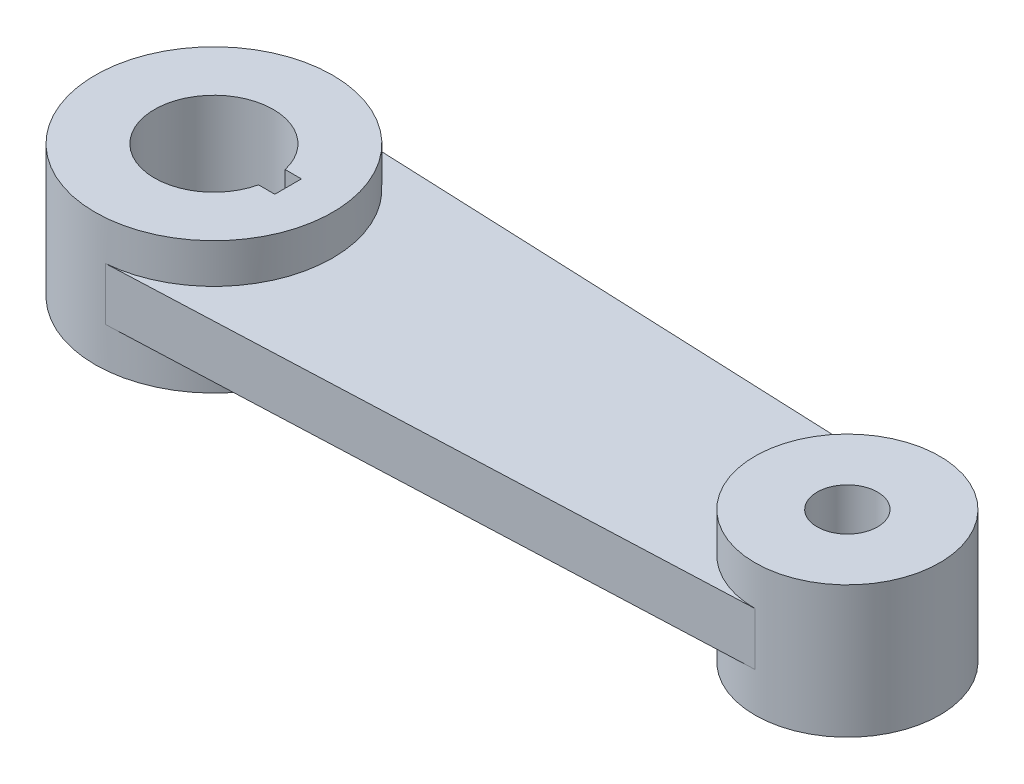
SolidWorks part; units mm, degrees
ref_plane "Front Plane" through (0, 0, 0) normal (0, 0, 1) x (1, 0, 0)
ref_plane "Top Plane" through (0, 0, 0) normal (0, 1, 0) x (1, 0, 0)
ref_plane "Right Plane" through (0, 0, 0) normal (1, 0, 0) x (0, 0, -1)
sketch "Sketch1" plane through (0, 0, 0) normal (0, 1, 0) x (1, 0, 0)
  line L1 (-150, 56.25) -> (150, 43.75)
  line L2 (-114.864, 6.3) -> (-114.864, -6.3)
  line L3 (-122.564, 6.3) -> (-114.864, 6.3)
  line L4 (-114.864, -6.3) -> (-122.564, -6.3)
  line L5 (150, -43.75) -> (-150, -56.25)
  arc A0 (-145.3206, 56.055) -> (-145.3206, -56.055) centre (-150, 0) ccw
  arc A1 (-122.564, 6.3) -> (-122.564, -6.3) centre (-150, 0) ccw
  circle A2 centre (150, 0) radius 21.9
  arc A3 (150, -43.75) -> (150, 43.75) centre (150, 0) ccw
  point P4 (0, 0)
  dimension "D1" = 112.5
  dimension "D2" = 56.3
  dimension "D6" = 43.8
  dimension "D7" = 87.5
  dimension "D4" = 7.7
  dimension "D5" = 12.6
extrude "Boss-Extrude3" add sketch "Sketch1" along normal mid plane 25 contours L5 A3 L1 A0 A1 L3 L2 L4 A2
sketch "Sketch2" plane through (0, 12.5, 0) normal (0, 1, 0) x (1, 0, 0)
  circle A0 centre (150, 0) radius 43.75
  circle A1 centre (-150, 0) radius 56.25
  dimension "D1" = 87.5
  dimension "D2" = 112.5
extrude "Boss-Extrude4" add sketch "Sketch2" along normal blind 18.75 and the other way blind 43.75
sketch "Sketch3" plane through (0, 31.25, 0) normal (0, 1, 0) x (1, 0, 0)
  line L0 (-114.864, -6.3) -> (-114.864, 6.3)
  line L1 (-122.564, -6.3) -> (-114.864, -6.3)
  line L2 (-122.564, 6.3) -> (-114.864, 6.3)
  circle A0 centre (150, 0) radius 14.301
  arc A1 (-122.564, 6.3) -> (-122.564, -6.3) centre (-150, 0) ccw
  dimension "D1" = 28.602
  dimension "D2" = 56.3
  dimension "D3" = 12.6
  dimension "D4" = 7.7
extrude "Cut-Extrude1" cut sketch "Sketch3" against normal through all
